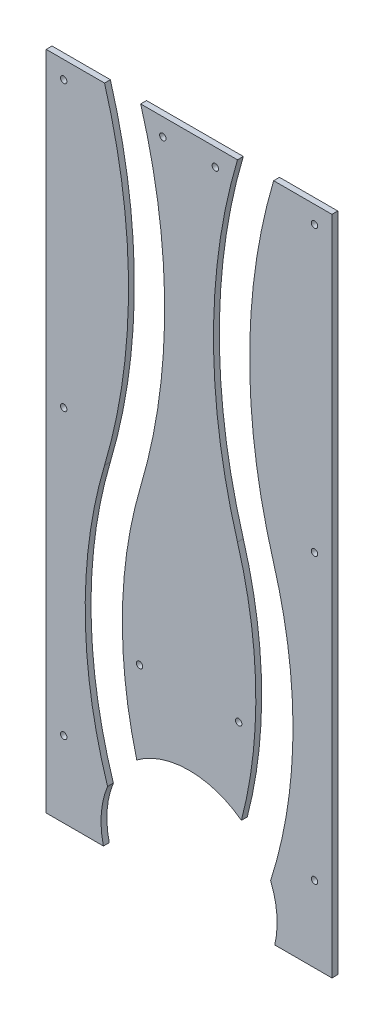
SolidWorks part; units mm, degrees
material "Contreplaqué pin"
ref_plane "Plan de face" through (0, 0, 0) normal (0, 0, 1) x (1, 0, 0)
ref_plane "Plan de dessus" through (0, 0, 0) normal (0, 1, 0) x (1, 0, 0)
ref_plane "Plan de droite" through (0, 0, 0) normal (1, 0, 0) x (0, 0, -1)
sketch "Esquisse1" plane through (0, 0, 0) normal (0, 0, 1) x (1, 0, 0)
  line L1 (0, 0) -> (245, 0)
  line L2 (0, 0) -> (0, 517)
  line L3 (0, 517) -> (245, 517)
  line L4 (245, 0) -> (245, 517)
  dimension "D1" = 245
  dimension "D2" = 517
extrude "Boss.-Extru.1" add sketch "Esquisse1" along normal blind 5
sketch "Esquisse6" [suppressed] plane through (0, 0, 0) normal (0, 0, 1) x (1, 0, 0)
  line L0 (245, 0) -> (245, 517) construction
  line L1 (0, 0) -> (245, 0)
  line L2 (0, 0) -> (0, -100)
  line L3 (0, -100) -> (245, -100)
  line L4 (245, 0) -> (245, -100)
  dimension "D1" = 100
extrude "Boss.-Extru.3" [suppressed] add sketch "Esquisse6" along normal blind 3
sketch "Esquisse2" [suppressed] plane through (0, 0, 3) normal (0, 0, 1) x (1, 0, 0)
  line L0 (245, 517) -> (0, 517) construction
  line L1 (0, 517) -> (0, -100) construction
  line L2 (40, 258.5) -> (77, 258.5) construction
  line L3 (122.5, 517) -> (122.5, 0) construction
  line L4 (0, 0) -> (245, 0) construction
  line L5 (40, 517) -> (77, 517)
  line L6 (40, -100) -> (77, -100)
  line L7 (205, -100) -> (168, -100)
  line L8 (205, 517) -> (168, 517)
  line L9 (0, -100) -> (245, -100) construction
  arc A0 (40, 517) -> (40, 258.5) centre (-338.5425, 387.75) cw
  arc A1 (77, 517) -> (77, 258.5) centre (-301.5425, 387.75) cw
  arc A2 (40, 258.5) -> (40, -100) centre (564.9806, 79.25) ccw
  arc A3 (77, 258.5) -> (77, -100) centre (601.9806, 79.25) ccw
  arc A4 (168, 258.5) -> (168, -100) centre (-356.9806, 79.25) cw
  arc A5 (205, 258.5) -> (205, -100) centre (-319.9806, 79.25) cw
  arc A6 (168, 517) -> (168, 258.5) centre (546.5425, 387.75) ccw
  arc A7 (205, 517) -> (205, 258.5) centre (583.5425, 387.75) ccw
  dimension "D4" = 400
  dimension "D1" = 40
  dimension "D2" = 258.5
  dimension "D3" = 37
extrude "Enlèv. mat.-Extru.2" [suppressed] cut sketch "Esquisse2" against normal up to next
sketch "Esquisse3" [suppressed] plane through (0, 0, 3) normal (0, 0, 1) x (1, 0, 0)
  line L0 (77, 0) -> (168, 0) construction
  circle A0 centre (122.5, 0) radius 75.5
  dimension "D1" = 151
extrude "Enlèv. mat.-Extru.3" [suppressed] cut sketch "Esquisse3" against normal up to next
hole_wizard "Dégagement M51" positions "Esquisse3D1" profile "Esquisse4" hole size "M5" standard "DIN" end condition through all
sketch3d "Esquisse3D1"
  line L0 (15, 502, 5) -> (15, 258.5, 5) construction
  line L1 (15, 258.5, 5) -> (15, 15, 5) construction
  line L2 (15, 15, 5) -> (230, 15, 5) construction
  line L3 (230, 15, 5) -> (230, 502, 5) construction
  line L4 (230, 502, 5) -> (145, 502, 5) construction
  line L5 (145, 502, 5) -> (100, 502, 5) construction
  line L6 (100, 502, 5) -> (15, 502, 5) construction
  line L9 (245, 517, 5) -> (0, 517, 5) construction
  line L10 (0, 517, 5) -> (0, 0, 5) construction
  line L11 (0, 0, 5) -> (245, 0, 5) construction
  line L12 (245, 0, 5) -> (245, 517, 5) construction
  line L13 (80, 100, 5) -> (15, 100, 5) construction
  line L15 (165, 100, 5) -> (230, 100, 5) construction
  point P0 (15, 502, 5)
  point P2 (15, 15, 5)
  point P4 (15, 258.5, 5)
  point P6 (100, 502, 5)
  point P8 (145, 502, 5)
  point P10 (80, 100, 5)
  point P12 (165, 100, 5)
  point P14 (230, 15, 5)
  point P16 (230, 258.5, 5)
  point P18 (230, 502, 5)
  point P40 (122.5, 0, 5)
  dimension "D1" = 15
  dimension "D2" = 15
  dimension "D3" = 15
  dimension "D4" = 15
  dimension "D5" = 85
  dimension "D6" = 65
  dimension "D7" = 85
sketch "Esquisse4" plane through (15, 502, 5) normal (1, 0, 0) x (0, -1, 0)
  line L0 (0, 0) -> (0, 5)
  line L1 (0, 5) -> (2.75, 5)
  line L2 (2.75, 5) -> (2.75, 0)
  line L5 (2.75, 0) -> (0, 0)
  line L11 (0, -6.35) -> (0, 107.95) construction
  dimension "Diamètre du perçage jusqu'au prochain" = 5.5
  dimension "Profondeur du perçage jusqu'au prochain" = 5
sketch "Esquisse5" plane through (0, 0, 0) normal (0, 0, 1) x (1, 0, 0)
  line L0 (245, 0) -> (245, 517) construction
  line L1 (0, 0) -> (245, 0)
  line L2 (0, 0) -> (0, -33)
  line L3 (0, -50) -> (245, -50)
  line L4 (245, 0) -> (245, -50)
  line L5 (0, -33) -> (-5, -33)
  line L6 (-5, -33) -> (-5, -50)
  line L7 (-5, -50) -> (0, -50)
  dimension "D1" = 50
  dimension "D2" = 17
  dimension "D3" = 5
extrude "Boss.-Extru.2" add sketch "Esquisse5" along normal blind 5
sketch "Esquisse7" plane through (0, 0, 5) normal (0, 0, 1) x (1, 0, 0)
  line L0 (245, 517) -> (0, 517) construction
  line L1 (245, 517) -> (0, 517) construction
  line L2 (-5, -50) -> (245, -50) construction
  line L3 (50, 233.1294) -> (50, 517) construction
  line L5 (0, 517) -> (0, -33) construction
  line L7 (81, 517) -> (81, 233.1294) construction
  line L8 (122.5, -50) -> (122.5, 517) construction
  line L10 (174.5, -50) -> (195, 233.1294) construction
  line L11 (195, 233.1294) -> (195, 517) construction
  line L12 (164, 517) -> (164, 233.1294) construction
  line L13 (50, 517) -> (81, 517)
  line L14 (164, 517) -> (195, 517)
  line L15 (70.5, -50) -> (107.5, -50)
  line L16 (137.5, -50) -> (174.5, -50)
  line L18 (-5, -50) -> (245, -50) construction
  arc A0 (50, 233.1294) -> (50, 517) centre (-429.4313, 375.0647) ccw
  arc A1 (50, 233.1294) -> (70.5, -50) centre (436.2266, 118.7873) ccw
  arc A2 (81, 233.1294) -> (81, 517) centre (-398.4313, 375.0647) ccw
  arc A3 (81, 233.1294) -> (107.5, -50) centre (447.4989, 124.6277) ccw
  arc A4 (164, 233.1294) -> (137.5, -50) centre (-202.4989, 124.6277) cw
  arc A5 (195, 233.1294) -> (174.5, -50) centre (-191.2266, 118.7873) cw
  arc A6 (195, 233.1294) -> (195, 517) centre (674.4313, 375.0647) cw
  arc A7 (164, 233.1294) -> (164, 517) centre (643.4313, 375.0647) cw
  point P57 (122.5, 517)
  dimension "D2" = 500
  dimension "D3" = 500
  dimension "D6" = 15
  dimension "D1" = 50
  dimension "D4" = 31
  dimension "D5" = 37
extrude "Enlèv. mat.-Extru.4" cut sketch "Esquisse7" against normal up to next and the other way through all
sketch "Esquisse9" plane through (0, 0, 5) normal (0, 0, 1) x (1, 0, 0)
  line L0 (174.5, -50) -> (245, -50) construction
  line L2 (122.5, -32.5) -> (122.5, -50) construction
  line L4 (164, 517) -> (81, 517) construction
  circle A0 centre (122.5, -32.5) radius 75.5
  point P14 (122.5, 517)
  dimension "D1" = 151
  dimension "D2" = 17.5
extrude "Enlèv. mat.-Extru.5" cut sketch "Esquisse9" against normal through all
sketch "Esquisse10" plane through (0, 0, 5) normal (0, 0, 1) x (1, 0, 0)
  line L0 (195.9439, -50) -> (245, -50) construction
  line L1 (200, -50) -> (240, -50)
  line L2 (200, -50) -> (200, 0)
  line L3 (210, 10) -> (230, 10)
  line L4 (240, -50) -> (240, 0)
  line L5 (220, 10) -> (220, -50) construction
  line L6 (245, 517) -> (195, 517) construction
  arc A0 (240, 0) -> (230, 10) centre (230, 0) ccw
  arc A1 (210, 10) -> (200, 0) centre (210, 0) ccw
  point P8 (240, 10)
  point P11 (200, 10)
  point P17 (220, 517)
  dimension "D3" = 10
  dimension "D1" = 60
  dimension "D2" = 40
extrude "Enlèv. mat.-Extru.6" [suppressed] cut sketch "Esquisse10" against normal up to next
sketch "Esquisse11" [suppressed] plane through (0, 0, 5) normal (0, 0, 1) x (1, 0, 0)
  line L0 (0, 467) -> (-5, 467)
  line L1 (0, 517) -> (0, -33) construction
  line L2 (-5, 467) -> (-5, 417)
  line L3 (-5, 417) -> (0, 417)
  line L4 (0, 417) -> (0, 467)
  line L5 (0, 367) -> (-5, 367)
  line L6 (-5, 367) -> (-5, 317)
  line L7 (-5, 317) -> (0, 317)
  line L8 (0, 317) -> (0, 367)
  line L9 (0, 267) -> (-5, 267)
  line L10 (-5, 267) -> (-5, 217)
  line L11 (-5, 217) -> (0, 217)
  line L12 (0, 167) -> (-5, 167)
  line L13 (-5, 167) -> (-5, 117)
  line L14 (-5, 117) -> (0, 117)
  line L15 (0, 117) -> (0, 167)
  line L16 (0, 217) -> (0, 267)
  line L17 (245, 517) -> (0, 517) construction
  line L18 (0, 67) -> (-5, 67)
  line L19 (-5, 67) -> (-5, 17)
  line L20 (-5, 17) -> (0, 17)
  line L21 (0, 67) -> (0, 17)
  dimension "D1" = 50
  dimension "D2" = 50
  dimension "D3" = 5
  dimension "D4" = 50
  dimension "D5" = 50
  dimension "D6" = 50
  dimension "D7" = 50
extrude "Boss.-Extru.4" [suppressed] add sketch "Esquisse11" against normal blind 5
hole_wizard "Dégagement M52" [suppressed] positions "Esquisse3D2" profile "Esquisse12" hole size "M5" standard "DIN"
sketch3d "Esquisse3D2"
  line L0 (152.5, -15, 0) -> (152.5, -40, 0) construction
  line L1 (152.5, -40, 0) -> (92.5, -40, 0) construction
  line L2 (92.5, -40, 0) -> (92.5, -15, 0) construction
  line L3 (92.5, -15, 0) -> (152.5, -15, 0) construction
  line L5 (142.5, -50, 0) -> (142.5, 0, 0) construction
  line L6 (142.5, -50, 0) -> (245, -50, 0) construction
  point P0 (152.5, -15, 0)
  point P2 (152.5, -40, 0)
  point P4 (92.5, -15, 0)
  point P6 (92.5, -40, 0)
  dimension "D1" = 10
  dimension "D2" = 60
  dimension "D3" = 25
  dimension "D4" = 10
sketch "Esquisse12" plane through (152.5, -15, 0) normal (1, 0, 0) x (0, 1, 0)
  line L0 (0, 0) -> (0, 5)
  line L1 (0, 5) -> (2.75, 5)
  line L2 (2.75, 5) -> (2.75, 0)
  line L5 (2.75, 0) -> (0, 0)
  line L11 (0, -6.35) -> (0, 107.95) construction
  dimension "Diamètre du perçage jusqu'au prochain" = 5.5
  dimension "Profondeur du perçage jusqu'au prochain" = 5
sketch "Esquisse13" plane through (0, 0, 0) normal (0, 0, -1) x (-1, 0, 0)
  line L1 (5, -50) -> (0, -50)
  line L2 (5, -50) -> (5, -33)
  line L3 (5, -33) -> (0, -33)
  line L4 (0, -50) -> (0, -33)
extrude "Enlèv. mat.-Extru.7" cut sketch "Esquisse13" against normal up to next
hole_wizard "Diamètre du perçage Ø4.5 (4.5)1" [suppressed] positions "Esquisse3D3" profile "Esquisse14" hole size "Ø4.5" standard "DIN"
sketch3d "Esquisse3D3"
  line L0 (0, 17, 0) -> (0, -33, 0) construction
  line L1 (245, -50, 0) -> (245, 517, 0) construction
  line L2 (142.5, -50, 0) -> (245, -50, 0) construction
  point P0 (60, -16, 0)
  point P2 (185, -16, 0)
  dimension "D1" = 78
  dimension "D2" = 53
  dimension "D3" = 78
  dimension "D4" = 53
sketch "Esquisse14" plane through (60, -16, 0) normal (1, 0, 0) x (0, 1, 0)
  line L0 (0, 0) -> (0, 5)
  line L1 (0, 5) -> (2.25, 5)
  line L2 (2.25, 5) -> (2.25, 0)
  line L5 (2.25, 0) -> (0, 0)
  line L11 (0, -6.35) -> (0, 107.95) construction
  dimension "Diamètre du perçage jusqu'au prochain" = 4.5
  dimension "Profondeur du perçage jusqu'au prochain" = 5
